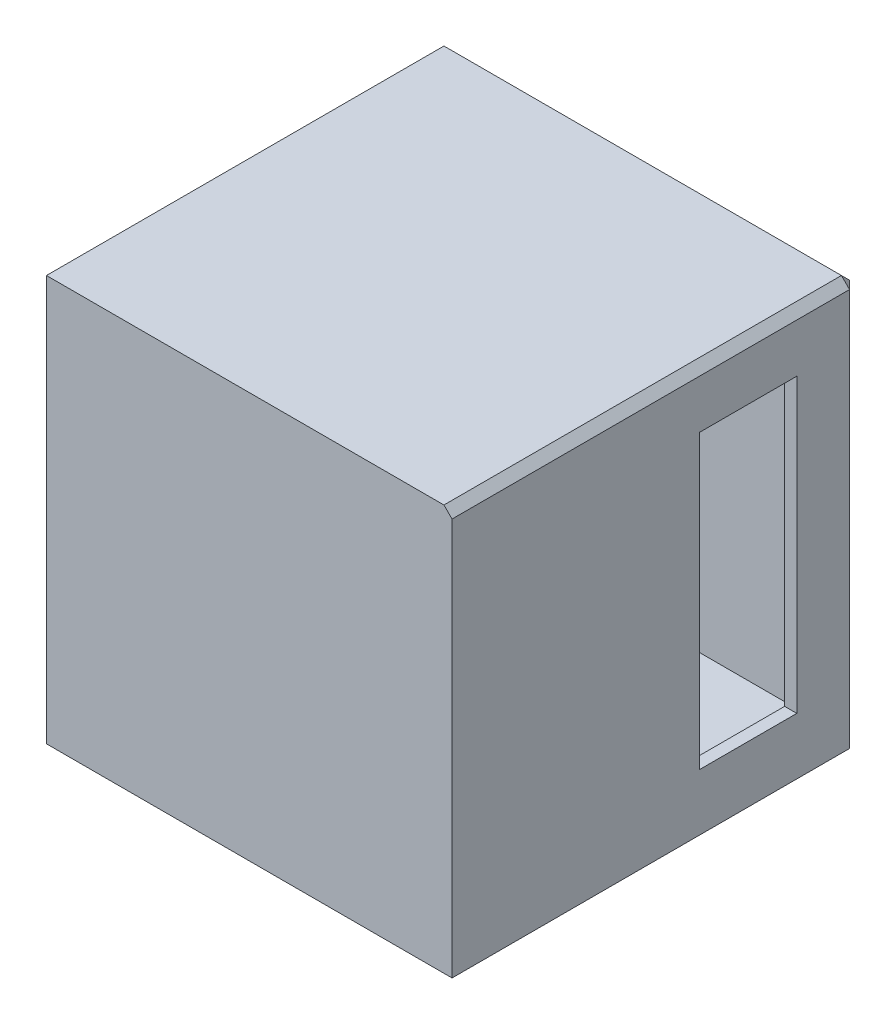
SolidWorks part; units mm, degrees
ref_plane "Plan de face" through (0, 0, 0) normal (0, 0, 1) x (1, 0, 0)
ref_plane "Plan de dessus" through (0, 0, 0) normal (0, 1, 0) x (1, 0, 0)
ref_plane "Plan de droite" through (0, 0, 0) normal (1, 0, 0) x (0, 0, -1)
sketch "Esquisse1" plane through (0, 0, 0) normal (0, 0, 1) x (1, 0, 0)
  line L1 (0, 100) -> (100, 100)
  line L2 (0, 100) -> (0, 0)
  line L3 (0, 0) -> (100, 0)
  line L4 (100, 100) -> (100, 0)
  dimension "D1" = 100
extrude "Boss.-Extru.1" add sketch "Esquisse1" along normal blind 3
sketch "Esquisse2" plane through (0, 0, 3) normal (0, 0, 1) x (1, 0, 0)
  line L1 (0, 100) -> (100, 100)
  line L2 (0, 100) -> (0, 0)
  line L3 (0, 0) -> (100, 0)
  line L4 (100, 100) -> (100, 0)
  line L5 (3, 97) -> (97, 97)
  line L6 (3, 97) -> (3, 3)
  line L7 (3, 3) -> (97, 3)
  line L8 (97, 97) -> (97, 3)
  dimension "D1" = 3
  dimension "D2" = 3
  dimension "D3" = 3
  dimension "D4" = 3
extrude "Boss.-Extru.2" add sketch "Esquisse2" along normal blind 94
sketch "Esquisse3" plane through (0, 0, 97) normal (0, 0, 1) x (1, 0, 0)
  line L1 (0, 100) -> (100, 100)
  line L2 (0, 100) -> (0, 0)
  line L3 (0, 0) -> (100, 0)
  line L4 (100, 100) -> (100, 0)
extrude "Boss.-Extru.3" add sketch "Esquisse3" along normal blind 3
sketch "Esquisse4" plane through (100, 0, 0) normal (1, 0, 0) x (0, 0, -1)
  line L0 (-100, 100) -> (0, 100) construction
  line L1 (-15, 86) -> (-39, 86)
  line L2 (-15, 86) -> (-15, 14)
  line L3 (-15, 14) -> (-39, 14)
  line L4 (-39, 86) -> (-39, 14)
  line L5 (-100, 0) -> (0, 0) construction
  line L6 (0, 0) -> (0, 100) construction
  dimension "D1" = 14
  dimension "D2" = 14
  dimension "D3" = 15
  dimension "D4" = 24
extrude "Enlèv. mat.-Extru.1" cut sketch "Esquisse4" against normal blind 3
chamfer "Chanfrein1" distance 2 angle 45 3 edges at (100, 100, 50) (100, 50, 0) (50, 100, 0)
